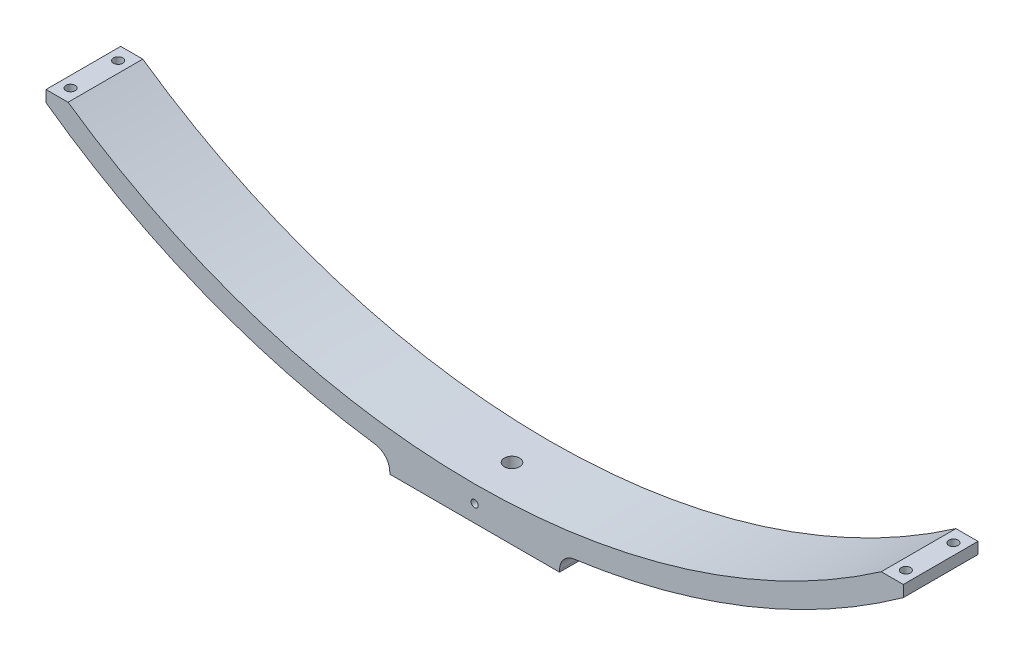
SolidWorks part; units mm, degrees
material "3.1325 (EN-AW 2017A)"
ref_plane "Plan de face" through (0, 0, 0) normal (0, 0, 1) x (1, 0, 0)
ref_plane "Plan de dessus" through (0, 0, 0) normal (0, 1, 0) x (1, 0, 0)
ref_plane "Plan de droite" through (0, 0, 0) normal (1, 0, 0) x (0, 0, -1)
sketch "Esquisse1" plane through (0, 0, 0) normal (0, 0, 1) x (1, 0, 0)
  line L0 (-252.5, 75) -> (-252.5, 68.2661)
  line L3 (-50, -10.1028) -> (-50, -20)
  line L4 (-50, -20) -> (50, -20)
  line L5 (252.5, 75) -> (239.5, 75)
  line L6 (50, -10.1028) -> (50, -20)
  line L7 (252.5, 75) -> (252.5, 68.2661)
  line L9 (-252.5, 75) -> (-239.5, 75)
  arc A0 (50, -10.1028) -> (252.5, 68.2661) centre (0, 419.9017) ccw
  arc A1 (-239.5, 75) -> (239.5, 75) centre (0, 419.9017) ccw
  arc A2 (-252.5, 68.2661) -> (-50, -10.1028) centre (0, 419.9017) ccw
  arc A3 (-246.9148, 64.322) -> (246.9148, 64.322) centre (0, 419.9017) ccw construction
  dimension "D3" = 50
  dimension "D1" = 252.5
  dimension "D2" = 50
  dimension "D5" = 13
extrude "Boss.-Extru.1" add sketch "Esquisse1" along normal blind 44
sketch "Esquisse2" plane through (0, -20, 0) normal (0, -1, 0) x (1, 0, 0)
  line L0 (-50, 44) -> (50, 44) construction
  circle A0 centre (0, 22) radius 4.5
  dimension "D1" = 22
extrude "Enlèv. mat.-Extru.1" cut sketch "Esquisse2" against normal through all
sketch "Esquisse6" plane through (0, 75, 0) normal (0, 1, 0) x (1, 0, 0)
  line L0 (252.5, 0) -> (239.5, 0) construction
  circle A0 centre (246, -8) radius 2.75
  dimension "D1" = 8
extrude "Enlèv. mat.-Extru.2" cut sketch "Esquisse6" against normal through all
ref_plane "Plan2" through (0, 45, 0) normal (0, 1, 0) x (-1, 0, 0)
sketch "Esquisse7" plane through (0, 45, 0) normal (0, 1, 0) x (-1, 0, 0)
  circle A0 centre (-246, 8) radius 4.75
extrude "Enlèv. mat.-Extru.3" cut sketch "Esquisse7" along normal blind 24
sketch "Esquisse8" plane through (0, 75, 0) normal (0, 1, 0) x (1, 0, 0)
  line L0 (252.5, -44) -> (239.5, -44) construction
  circle A0 centre (246, -36) radius 2.75
  dimension "D1" = 8
extrude "Enlèv. mat.-Extru.4" cut sketch "Esquisse8" against normal through all
sketch "Esquisse9" plane through (0, 45, 0) normal (0, 1, 0) x (-1, 0, 0)
  circle A0 centre (-246, 36) radius 4.75
  circle A2 centre (-246, 36) radius 2.75 construction
  dimension "D1" = 0
  dimension "D2" = 0
extrude "Enlèv. mat.-Extru.5" cut sketch "Esquisse9" along normal blind 24
sketch "Esquisse10" plane through (0, 75, 0) normal (0, 1, 0) x (1, 0, 0)
  line L0 (-239.5, 0) -> (-252.5, 0) construction
  line L1 (-239.5, -44) -> (-252.5, -44) construction
  circle A0 centre (-246, -8) radius 2.75
  circle A1 centre (-246, -36) radius 2.75
  dimension "D1" = 8
  dimension "D2" = 8
extrude "Enlèv. mat.-Extru.6" cut sketch "Esquisse10" against normal through all
sketch "Esquisse11" plane through (0, 45, 0) normal (0, 1, 0) x (-1, 0, 0)
  circle A0 centre (246, 8) radius 4.75
extrude "Enlèv. mat.-Extru.8" cut sketch "Esquisse11" along normal blind 24
sketch "Esquisse13" plane through (0, 45, 0) normal (0, 1, 0) x (-1, 0, 0)
  circle A0 centre (245.7951, 35.6371) radius 4.75
extrude "Enlèv. mat.-Extru.11" cut sketch "Esquisse13" along normal blind 24
hole_wizard "Trou taraudé M51" positions "Esquisse15" profile "Esquisse14" tap size "M5" standard "ISO" end condition through all
sketch "Esquisse15" plane through (0, 0, 0) normal (0, 0, -1) x (-1, 0, 0)
  line L0 (0, 0) -> (0, -20) construction
  line L1 (50, -20) -> (-50, -20) construction
  point P0 (0, -10)
  dimension "D1" = 0
  dimension "D2" = 10
sketch "Esquisse14" plane through (0, -10, 0) normal (1, 0, 0) x (0, 1, 0)
  line L0 (0, 0) -> (0, 44)
  line L1 (0, 44) -> (2.1, 44)
  line L2 (2.1, 44) -> (2.1, 0)
  line L5 (2.1, 0) -> (0, 0)
  line L11 (0, -6.35) -> (0, 107.95) construction
  dimension "Diamètre du trou pour taraudage jusqu'au prochain" = 4.2
  dimension "Profondeur du trou pour taraudage jusqu'au prochain" = 44
cosmetic thread "Filetage de perçage1" parameters "D2"=5
fillet "Congé1" radius 10 2 edges at (50, -10.1028, 22) (-50, -10.1028, 22)
